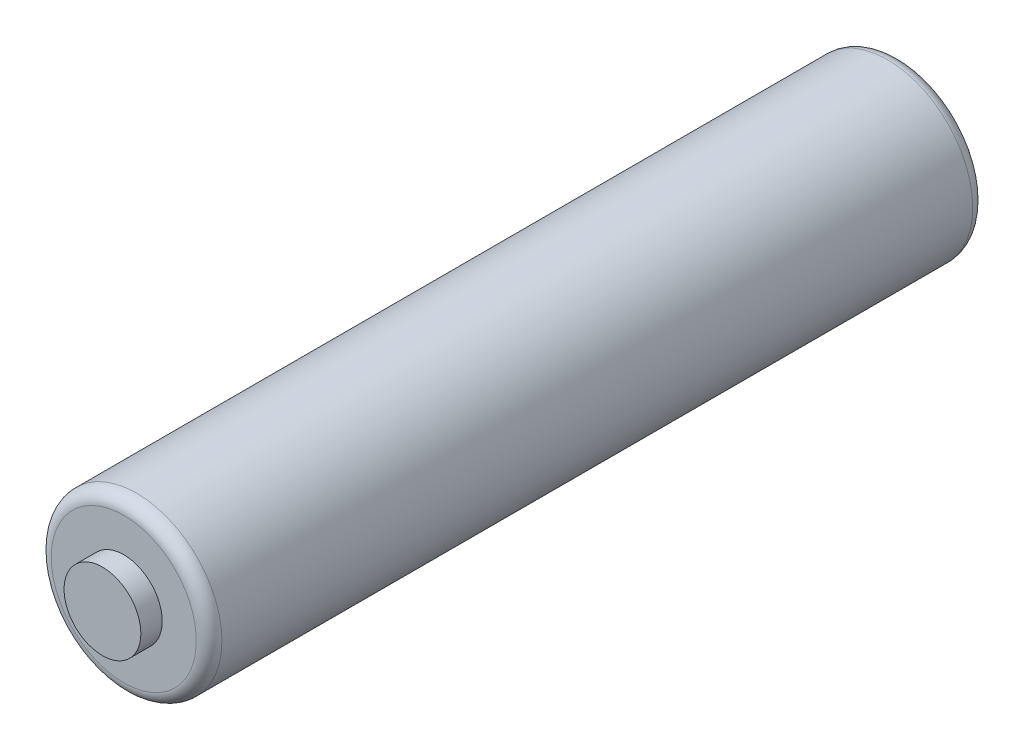
SolidWorks part; units mm, degrees
ref_plane "Front Plane" through (0, 0, 0) normal (0, 0, 1) x (1, 0, 0)
ref_plane "Top Plane" through (0, 0, 0) normal (0, 1, 0) x (1, 0, 0)
ref_plane "Right Plane" through (0, 0, 0) normal (1, 0, 0) x (0, 0, -1)
sketch "Sketch1" plane through (0, 0, 0) normal (1, 0, 0) x (0, 0, -1)
  line L0 (-152.4, 7.1437) -> (152.4, -7.1438) construction
  line L1 (-152.4, -7.1438) -> (152.4, -7.1438)
  line L2 (-152.4, -7.1438) -> (-152.4, 7.1437)
  line L3 (-152.4, 7.1437) -> (152.4, 7.1437) construction
  line L4 (152.4, -7.1438) -> (152.4, 7.1437)
  line L5 (-152.4, 7.1437) -> (-144.4625, 7.1437)
  line L6 (-144.4625, 7.1437) -> (144.4625, 7.1437) construction
  line L7 (-144.4625, 7.1437) -> (-144.4625, 24.6062)
  line L8 (-144.4625, 24.6062) -> (144.4625, 24.6062)
  line L9 (144.4625, 7.1437) -> (144.4625, 24.6062)
  line L10 (152.4, 7.1437) -> (144.4625, 7.1437)
  dimension "D1" = 14.2875
  dimension "D2" = 304.8
  dimension "D3" = 17.4625
  dimension "D4" = 7.9375
revolve "Revolve1" add sketch "Sketch1" angle 360 about L1
fillet "Fillet1" radius 4.7625 2 edges at (31.75, -7.1438, -144.4625) (31.75, -7.1438, 144.4625)
